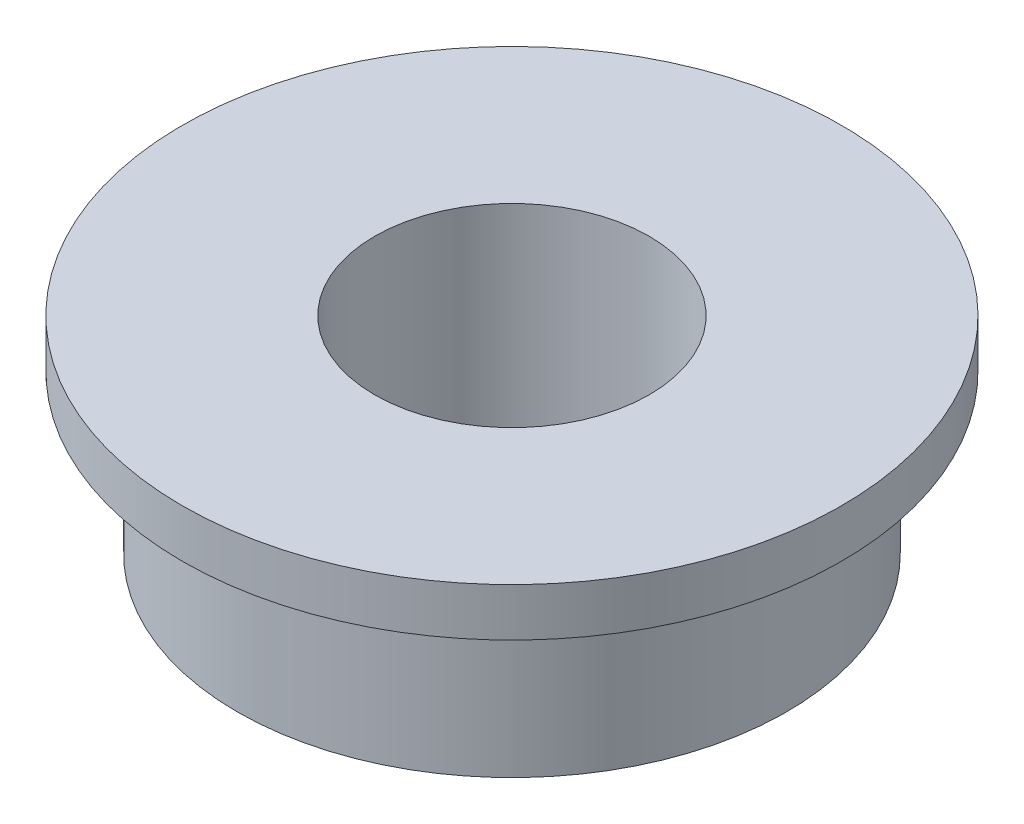
SolidWorks part; units mm, degrees
material "Aluminum Bronze"
ref_plane "Front Plane" through (0, 0, 0) normal (0, 0, 1) x (1, 0, 0)
ref_plane "Top Plane" through (0, 0, 0) normal (0, 1, 0) x (1, 0, 0)
ref_plane "Right Plane" through (0, 0, 0) normal (1, 0, 0) x (0, 0, -1)
sketch "Sketch1" plane through (0, 0, 0) normal (0, 1, 0) x (1, 0, 0)
  circle A0 centre (0, 0) radius 2
  circle A1 centre (0, 0) radius 4
  dimension "D1" = 4
  dimension "D2" = 8
extrude "Boss-Extrude1" add sketch "Sketch1" along normal blind 3
sketch "Sketch2" plane through (0, 3, 0) normal (0, 1, 0) x (-1, 0, 0)
  circle A0 centre (0, 0) radius 2.5
  circle A1 centre (0, 0) radius 4.8
  dimension "D1" = 9.6
  dimension "D2" = 5
extrude "Boss-Extrude2" add sketch "Sketch2" against normal blind 0.7
